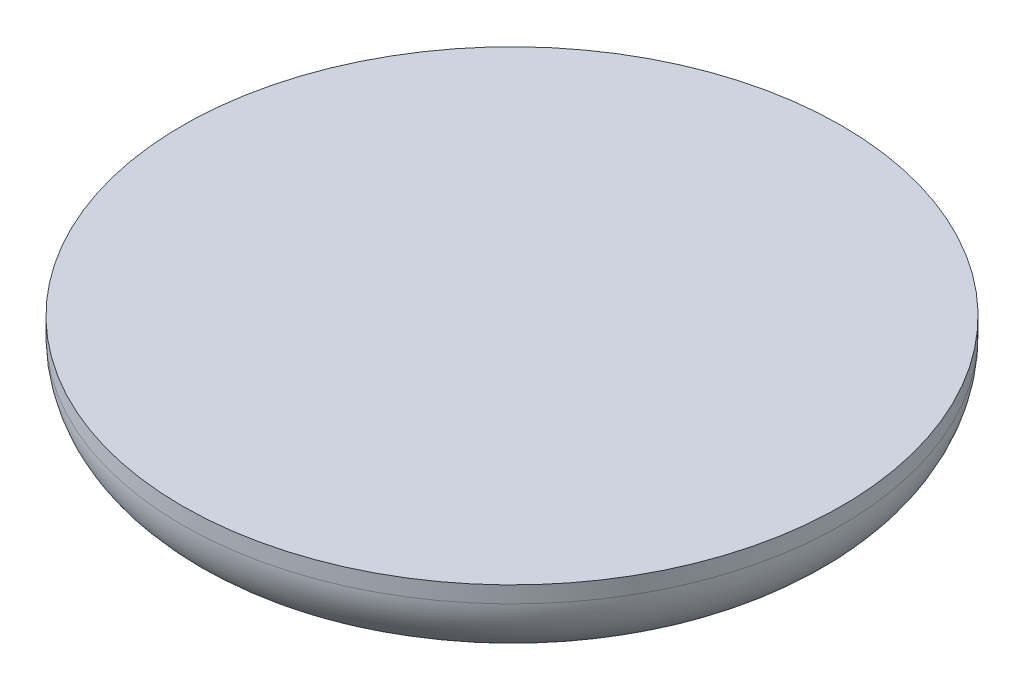
SolidWorks part; units mm, degrees
ref_plane "Front Plane" through (0, 0, 0) normal (0, 0, 1) x (1, 0, 0)
ref_plane "Top Plane" through (0, 0, 0) normal (0, 1, 0) x (1, 0, 0)
ref_plane "Right Plane" through (0, 0, 0) normal (1, 0, 0) x (0, 0, -1)
sketch "Sketch1" plane through (0, 0, 0) normal (0, 1, 0) x (1, 0, 0)
  circle A0 centre (0, 0) radius 20
  dimension "D1" = 40
extrude "Boss-Extrude1" add sketch "Sketch1" along normal blind 5
fillet "Fillet1" radius 4 1 edges at (0, 0, 20)
